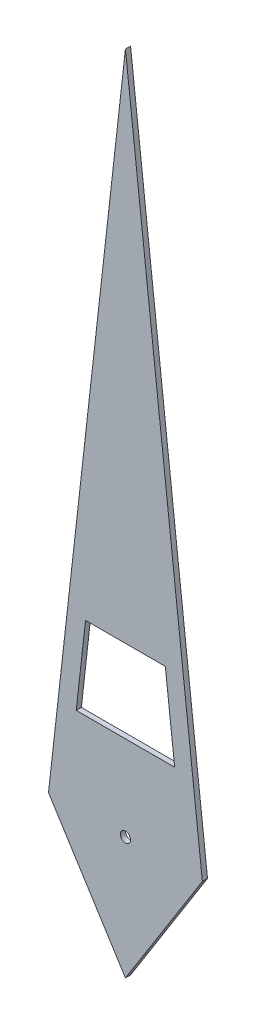
SolidWorks part; units mm, degrees
ref_plane "Front Plane" through (0, 0, 0) normal (0, 0, 1) x (1, 0, 0)
ref_plane "Top Plane" through (0, 0, 0) normal (0, 1, 0) x (1, 0, 0)
ref_plane "Right Plane" through (0, 0, 0) normal (1, 0, 0) x (0, 0, -1)
sketch "Sketch1" plane through (0, 0, 0) normal (0, 0, 1) x (1, 0, 0)
  line L0 (0, 0) -> (0, 13.3029) construction
  line L1 (0, 13.3029) -> (1.5, 0)
  line L2 (1.5, 0) -> (0, -2.3803)
  line L3 (-1.5, 0) -> (0, -2.3803)
  line L4 (0, 13.3029) -> (-1.5, 0)
  circle A0 centre (0, 0) radius 0.1
  dimension "D1" = 0.2
  dimension "D2" = 3
extrude "Boss-Extrude1" add sketch "Sketch1" along normal blind 0.1
sketch "Sketch2" plane through (0, 0, 0.1) normal (0, 0, 1) x (1, 0, 0)
  line L0 (-0.9592, 1.6581) -> (0.9592, 1.6581)
  line L1 (0.9592, 1.6581) -> (0.7776, 3.2683)
  line L2 (0, 0) -> (0, 3.2542) construction
  line L3 (1.5, 0) -> (0, 13.3029) construction
  line L4 (-0.9592, 1.6581) -> (-0.7776, 3.2683)
  line L5 (0, 13.3029) -> (-1.5, 0) construction
  line L6 (-0.7776, 3.2683) -> (0.7776, 3.2683)
extrude "Cut-Extrude1" cut sketch "Sketch2" against normal blind 0.1
